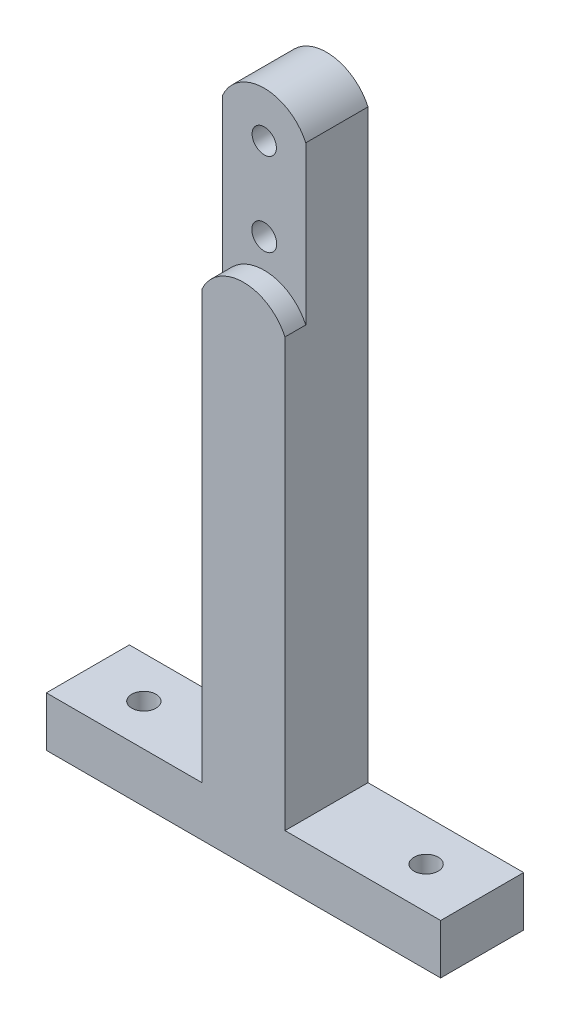
SolidWorks part; units mm, degrees
ref_plane "Front Plane" through (0, 0, 0) normal (0, 0, 1) x (1, 0, 0)
ref_plane "Top Plane" through (0, 0, 0) normal (0, 1, 0) x (1, 0, 0)
ref_plane "Right Plane" through (0, 0, 0) normal (1, 0, 0) x (0, 0, -1)
sketch "Sketch1" plane through (0, 0, 0) normal (0, 0, 1) x (1, 0, 0)
  line L0 (-10, -128.2474) -> (-10, -269.2474)
  line L1 (10, -128.2474) -> (10, -269.2474)
  line L2 (10, -269.2474) -> (47.5, -269.2474)
  line L3 (-47.5, -269.2474) -> (-10, -269.2474)
  line L4 (-47.5, -269.2474) -> (-47.5, -281.2474)
  line L5 (-47.5, -281.2474) -> (47.5, -281.2474)
  line L6 (47.5, -269.2474) -> (47.5, -281.2474)
  line L7 (-10, -269.2474) -> (10, -269.2474) construction
  line L8 (0, -269.2474) -> (0, -121.83) construction
  arc A0 (-10, -128.2474) -> (10, -128.2474) centre (0, -132.83) cw
  circle A1 centre (0, -152.83) radius 3 construction
  circle A2 centre (0, -132.83) radius 2.925 construction
  circle A3 centre (0, -152.83) radius 3
  circle A4 centre (0, -132.83) radius 2.925
  point P17 (0, -152.83)
  point P20 (0, -132.83)
  dimension "D3" = 12
  dimension "D1" = 20
  dimension "D2" = 20
  dimension "D4" = 141
  dimension "D5" = 95
  dimension "D6" = 11
extrude "Boss-Extrude1" add sketch "Sketch1" along normal blind 20
sketch "Sketch2" plane through (0, 0, 20) normal (0, 0, 1) x (1, 0, 0)
  line L0 (-10, -128.2474) -> (-10, -166.2474)
  line L1 (-10, -128.2474) -> (-10, -269.2474) construction
  line L2 (10, -128.2474) -> (10, -166.2474)
  line L3 (10, -269.2474) -> (10, -128.2474) construction
  arc A0 (10, -128.2474) -> (-10, -128.2474) centre (0, -132.83) ccw construction
  arc A1 (10, -128.2474) -> (-10, -128.2474) centre (0, -132.83) ccw
  arc A2 (-10, -166.2474) -> (10, -166.2474) centre (0, -170.83) cw
  dimension "D1" = 11
  dimension "D2" = 38
extrude "Cut-Extrude1" cut sketch "Sketch2" against normal blind 5
sketch "Sketch3" plane through (0, -269.2474, 0) normal (0, 1, 0) x (1, 0, 0)
  line L0 (-34, -10) -> (34, -10) construction
  line L1 (47.5, -20) -> (47.5, 0) construction
  circle A0 centre (-34, -10) radius 2.925
  circle A1 centre (34, -10) radius 2.925
  point P2 (0, -10)
  point P9 (47.5, -10)
  dimension "D2" = 5.85
  dimension "D1" = 68
extrude "Cut-Extrude2" cut sketch "Sketch3" against normal through all
sketch "Sketch4" plane through (0, -281.2474, 0) normal (0, -1, 0) x (1, 0, 0)
  line L0 (-47.5, 10) -> (47.5, 10) construction
  line L1 (-47.5, 20) -> (-47.5, 0) construction
  line L2 (47.5, 20) -> (47.5, 0) construction
  line L3 (0, 20) -> (0, 0) construction
  line L4 (-47.5, 20) -> (47.5, 20) construction
  point P11 (0, 10)
  point P12 (34, 10)
  point P13 (-34, 10)
sketch "Sketch5" plane through (0, 0, 0) normal (0, 0, -1) x (-1, 0, 0)
  line L0 (0, -281.2474) -> (0, -105.7405) construction
  point P4 (0, -132.83)
  point P5 (0, -152.83)
